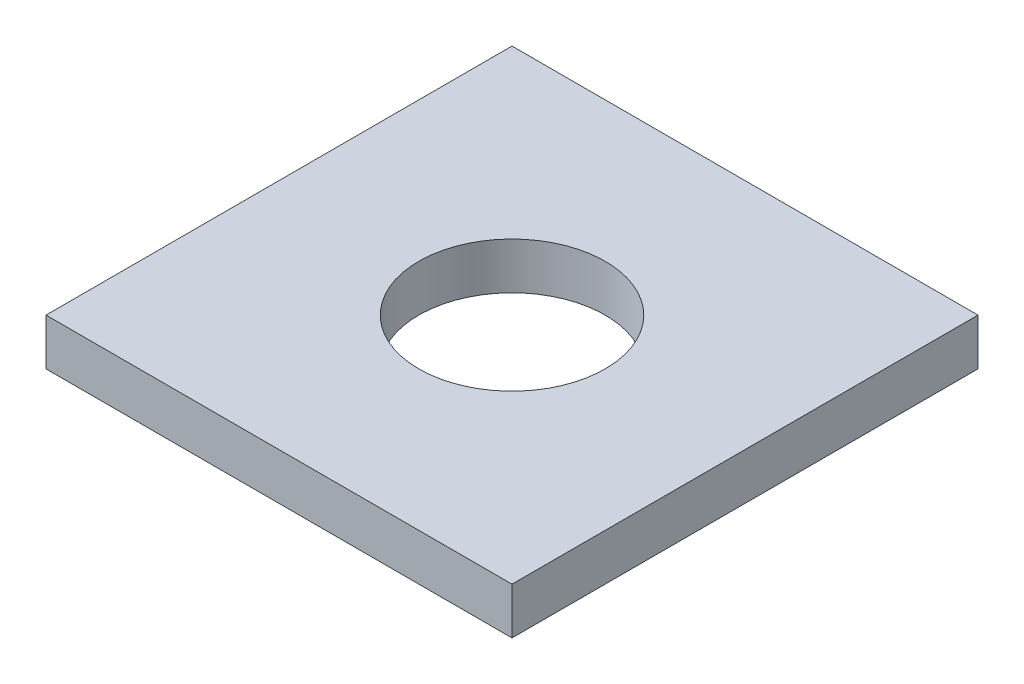
SolidWorks part; units mm, degrees
material "Plain Carbon Steel"
ref_plane "Front Plane" through (0, 0, 0) normal (0, 0, 1) x (1, 0, 0)
ref_plane "Top Plane" through (0, 0, 0) normal (0, 1, 0) x (1, 0, 0)
ref_plane "Right Plane" through (0, 0, 0) normal (1, 0, 0) x (0, 0, -1)
sketch "Sketch1" plane through (0, 0, 0) normal (0, 1, 0) x (1, 0, 0)
  line L1 (15.875, 15.875) -> (-15.875, 15.875)
  line L2 (15.875, 15.875) -> (15.875, -15.875)
  line L3 (15.875, -15.875) -> (-15.875, -15.875)
  line L4 (-15.875, 15.875) -> (-15.875, -15.875)
  line L5 (15.875, 15.875) -> (-15.875, -15.875) construction
  line L6 (15.875, -15.875) -> (-15.875, 15.875) construction
  circle A0 centre (0, 0) radius 6.35
  point P0 (0, 0)
  dimension "D3" = 12.7
  dimension "D1" = 31.75
  dimension "D2" = 31.75
extrude "Boss-Extrude1" add sketch "Sketch1" along normal mid plane 3.175
